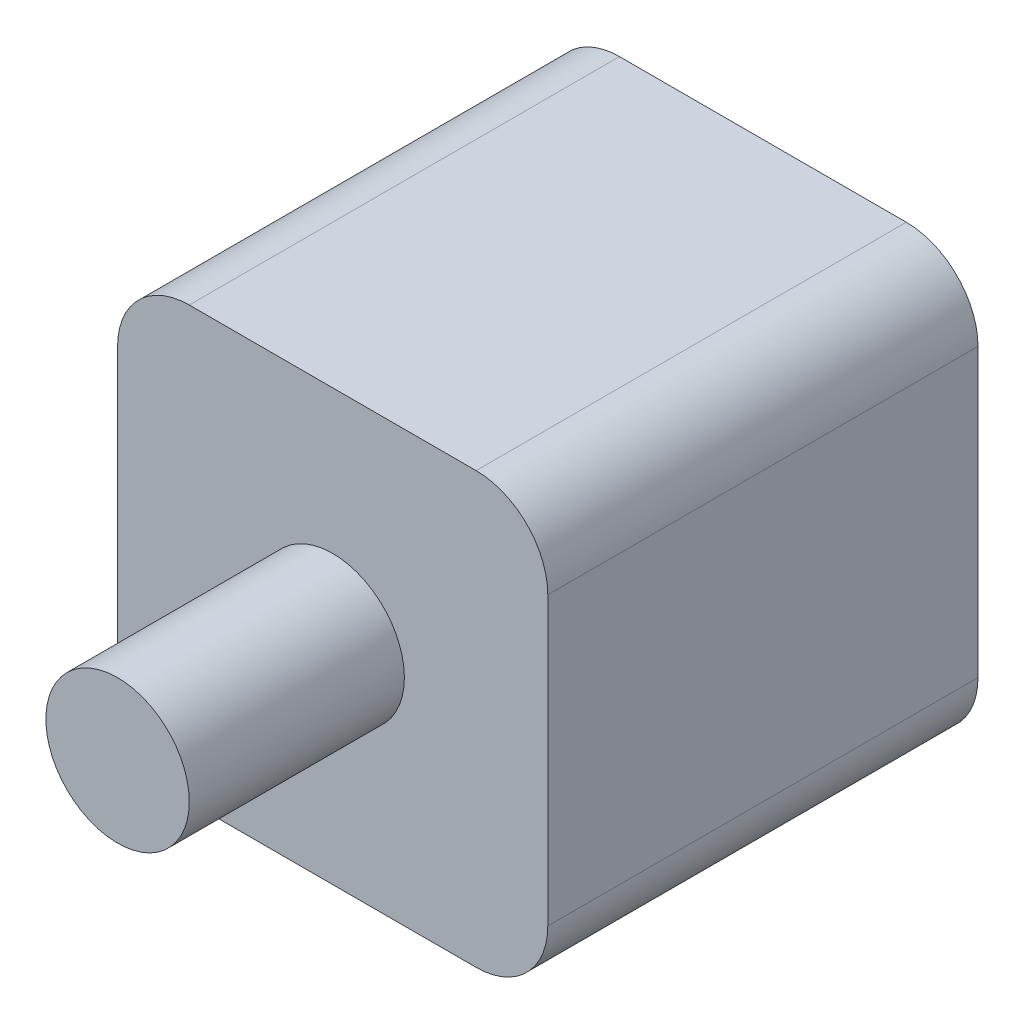
SolidWorks part; units mm, degrees
material "Plain Carbon Steel"
ref_plane "Front Plane" through (0, 0, 0) normal (0, 0, 1) x (1, 0, 0)
ref_plane "Top Plane" through (0, 0, 0) normal (0, 1, 0) x (1, 0, 0)
ref_plane "Right Plane" through (0, 0, 0) normal (1, 0, 0) x (0, 0, -1)
sketch "Sketch1" plane through (0, 0, 0) normal (0, 0, 1) x (1, 0, 0)
  line L1 (-30, 30) -> (30, 30)
  line L2 (-30, 30) -> (-30, -30)
  line L3 (-30, -30) -> (30, -30)
  line L4 (30, 30) -> (30, -30)
  line L5 (-30, 30) -> (30, -30) construction
  line L6 (-30, -30) -> (30, 30) construction
  point P0 (0, 0)
  dimension "D1" = 60
  dimension "D2" = 60
extrude "Boss-Extrude1" add sketch "Sketch1" along normal mid plane 60
sketch "Sketch2" plane through (0, 0, 30) normal (0, 0, 1) x (1, 0, 0)
  circle A0 centre (0, 0) radius 10
  dimension "D1" = 20
extrude "Boss-Extrude2" add sketch "Sketch2" along normal blind 30
fillet "Fillet1" radius 10 4 edges at (-30, -30, 0) (30, -30, 0) (-30, 30, 0) (30, 30, 0)
